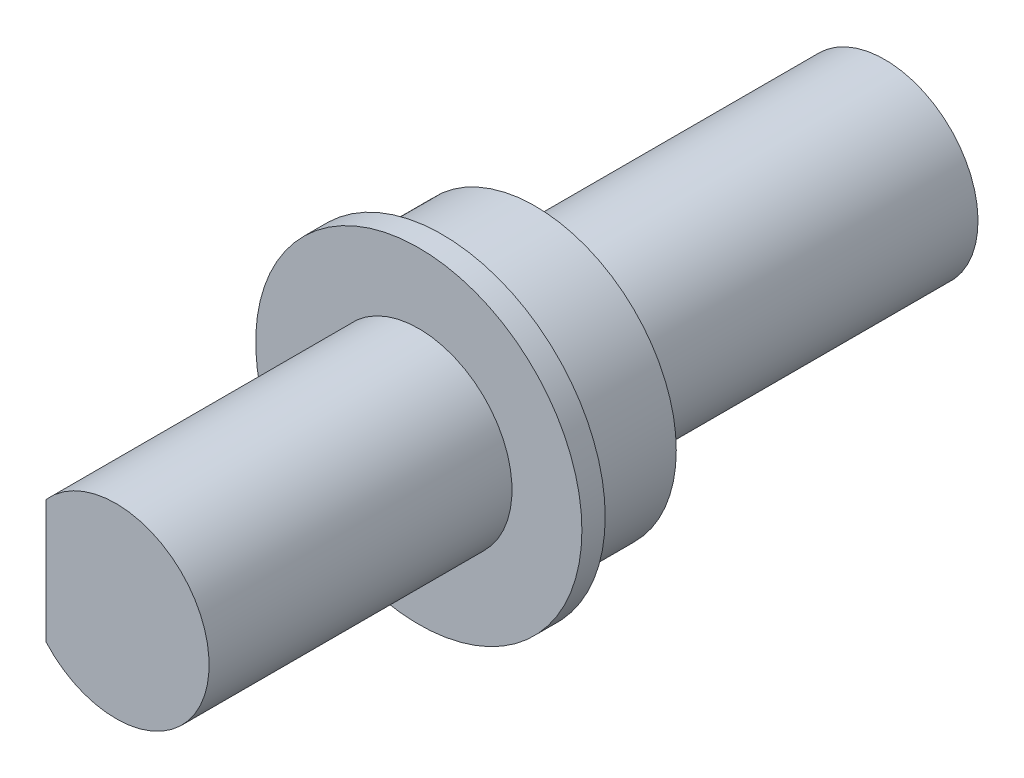
SolidWorks part; units mm, degrees
ref_plane "前视基准面" through (0, 0, 0) normal (0, 0, 1) x (1, 0, 0)
ref_plane "上视基准面" through (0, 0, 0) normal (0, 1, 0) x (1, 0, 0)
ref_plane "右视基准面" through (0, 0, 0) normal (1, 0, 0) x (0, 0, -1)
sketch "草图1" plane through (0, 0, 0) normal (0, 0, 1) x (1, 0, 0)
  circle A0 centre (0, 0) radius 6.05
  dimension "D1" = 12.1
extrude "凸台-拉伸1" add sketch "草图1" along normal blind 5
sketch "草图7" plane through (0, 0, 5) normal (0, 0, 1) x (1, 0, 0)
  circle A0 centre (0, 0) radius 7
  dimension "D1" = 14
extrude "凸台-拉伸6" add sketch "草图7" against normal blind 1
sketch "草图2" plane through (0, 0, 5) normal (0, 0, 1) x (1, 0, 0)
  line L0 (-3, 2.6458) -> (-3, -2.6458)
  circle A1 centre (0, 0) radius 4
  dimension "D2" = 8
  dimension "D1" = 3
extrude "凸台-拉伸2" add sketch "草图2" along normal blind 13 contours L0 A1
sketch "草图4" plane through (0, 0, 0) normal (0, 0, -1) x (-1, 0, 0)
  line L0 (-2.6458, -3) -> (2.6458, -3)
  circle A0 centre (0, 0) radius 4
  dimension "D1" = 8
  dimension "D2" = 3
extrude "凸台-拉伸3" add sketch "草图4" along normal blind 15 contours L0 A0
